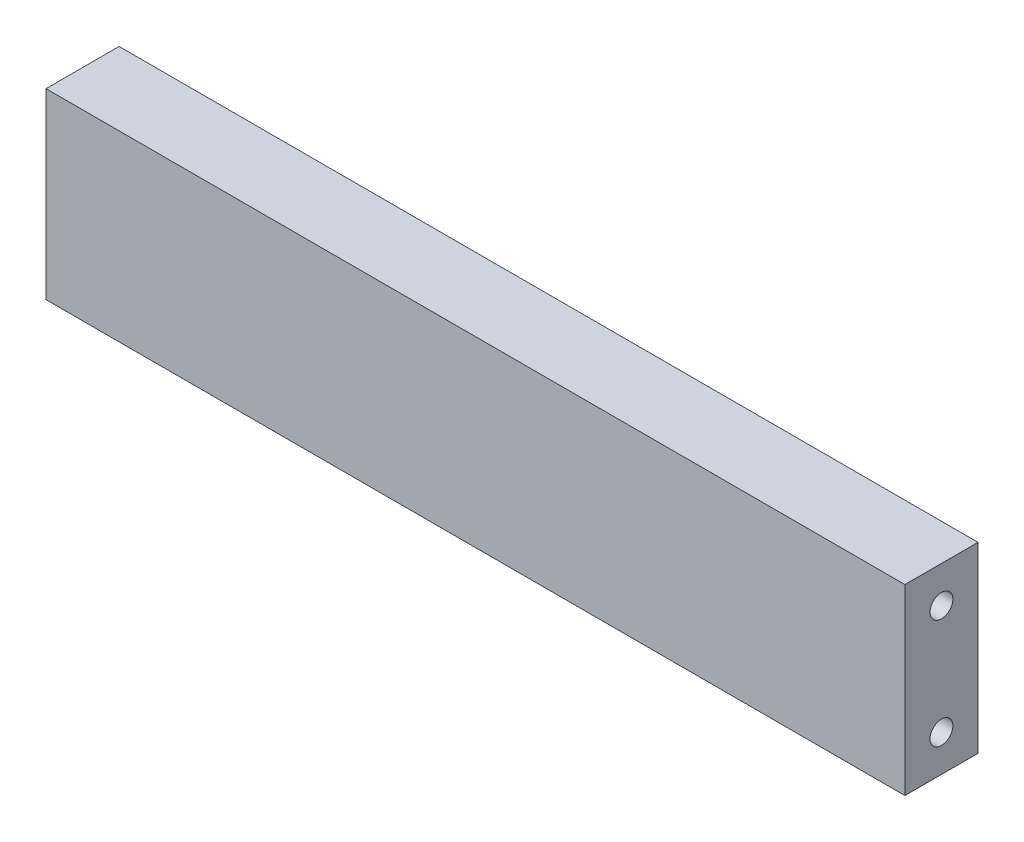
SolidWorks part; units mm, degrees
ref_plane "정면" through (0, 0, 0) normal (0, 0, 1) x (1, 0, 0)
ref_plane "윗면" through (0, 0, 0) normal (0, 1, 0) x (1, 0, 0)
ref_plane "우측면" through (0, 0, 0) normal (1, 0, 0) x (0, 0, -1)
sketch "스케치1" plane through (0, 0, 0) normal (0, 0, 1) x (1, 0, 0)
  line L1 (-47, 10) -> (47, 10)
  line L2 (-47, 10) -> (-47, -10)
  line L3 (-47, -10) -> (47, -10)
  line L4 (47, 10) -> (47, -10)
  line L5 (-47, 10) -> (47, -10) construction
  line L6 (-47, -10) -> (47, 10) construction
  point P0 (0, 0)
  dimension "D1" = 94
  dimension "D2" = 20
extrude "보스-돌출1" add sketch "스케치1" along normal blind 8
hole_wizard "M3-HORIZONTALBAR_FIX" positions "스케치4" profile "스케치5" tap size "M3" standard "ISO"
sketch "스케치4" plane through (47, 0, 0) normal (1, 0, 0) x (0, 0, -1)
  line L0 (-4, 6) -> (-4, -6)
  line L2 (0, -10) -> (0, 10) construction
  line L3 (-8, 10) -> (0, 10) construction
  point P0 (-4, 6)
  point P2 (-4, -6)
  point P9 (-4, 0)
  point P12 (0, 0)
  point P15 (-4, 10)
  dimension "D1" = 4
sketch "스케치5" plane through (47, 6, 4) normal (0, 1, 0) x (0, 0, -1)
  line L0 (0, 0) -> (0, 9.2511)
  line L1 (0, 9.2511) -> (1.25, 8.5)
  line L2 (1.25, 8.5) -> (1.25, 0)
  line L5 (1.25, 0) -> (0, 0)
  line L10 (0, 9.2511) -> (-1.25, 8.5) construction
  line L11 (0, -6.35) -> (0, 107.95) construction
  dimension "탭 드릴 지름" = 2.5
  dimension "탭 드릴 깊이" = 8.5
  dimension "드릴 각도" = 118
cosmetic thread "구멍 나사산2" parameters "D1"=6, "D2"=3
cosmetic thread "구멍 나사산3" parameters "D1"=6, "D2"=3
ref_plane "평면1" through (0, 0, 0) normal (1, 0, 0) x (0, 0, -1)
mirror "대칭 복사1" about plane through (0, 0, 0) normal (1, 0, 0) of "M3-HORIZONTALBAR_FIX"
cosmetic thread "구멍 나사산4" parameters "D1"=6, "D2"=3
cosmetic thread "구멍 나사산5" parameters "D1"=6, "D2"=3
